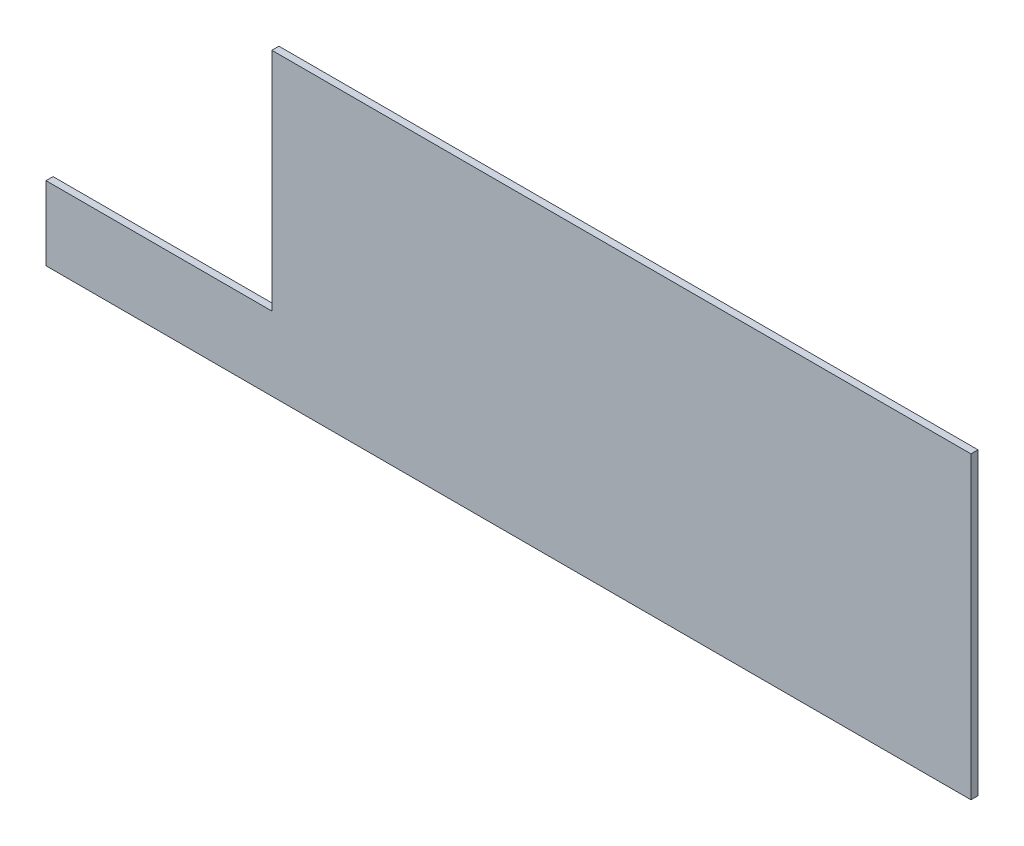
SolidWorks part; units mm, degrees
ref_plane "Front Plane" through (0, 0, 0) normal (0, 0, 1) x (1, 0, 0)
ref_plane "Top Plane" through (0, 0, 0) normal (0, 1, 0) x (1, 0, 0)
ref_plane "Right Plane" through (0, 0, 0) normal (1, 0, 0) x (0, 0, -1)
sketch "Sketch1" plane through (0, 0, 0) normal (0, 0, 1) x (1, 0, 0)
  line L0 (-24.0747, 111.1485) -> (-24.0747, 9.5485)
  line L1 (-24.0747, 111.1485) -> (290.4053, 111.1485)
  line L4 (290.4053, 111.1485) -> (290.4053, -23.6265)
  line L5 (-24.0747, 9.5485) -> (-125.6747, 9.5485)
  line L6 (-125.6747, 9.5485) -> (-125.6747, -23.6265)
  line L7 (-125.6747, -23.6265) -> (290.4053, -23.6265)
extrude "Boss-Extrude1" add sketch "Sketch1" along normal blind 3.175
